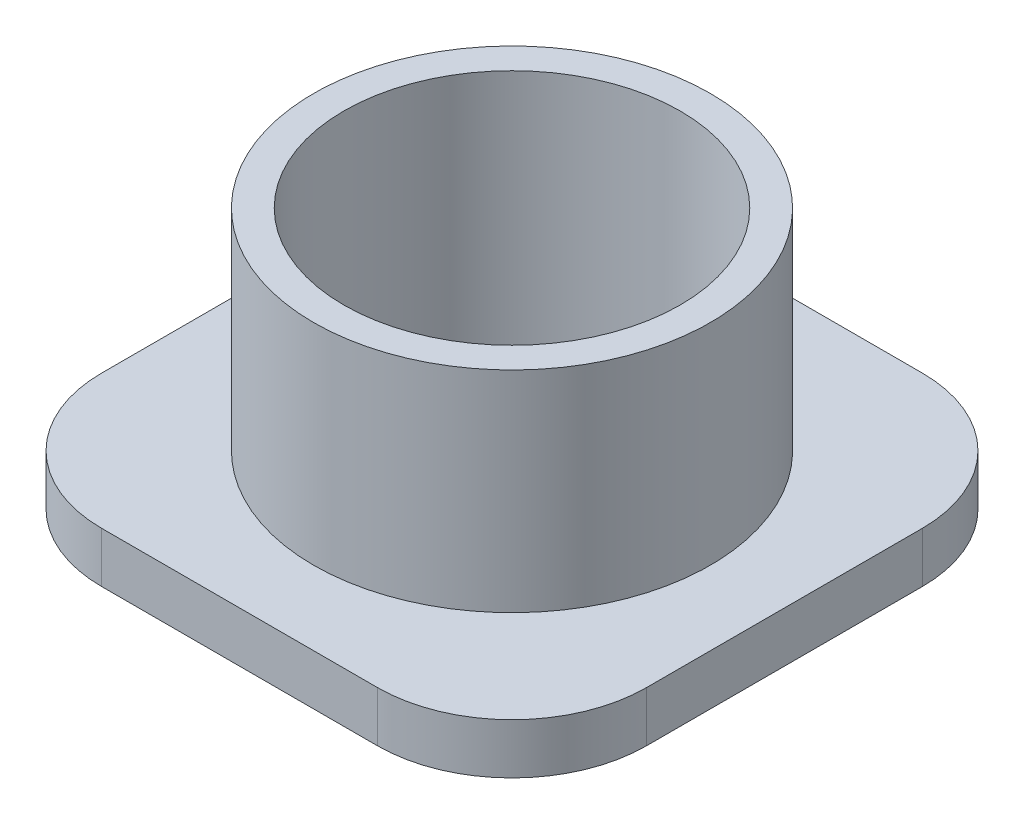
SolidWorks part; units mm, degrees
ref_plane "YZ" through (0, 0, 0) normal (0, 0, 1) x (1, 0, 0)
ref_plane "XY" through (0, 0, 0) normal (0, 1, 0) x (1, 0, 0)
ref_plane "XZ" through (0, 0, 0) normal (1, 0, 0) x (0, 0, -1)
sketch "Sketch1" plane through (0, 0, 0) normal (0, 1, 0) x (1, 0, 0)
  line L0 (-10.414, 20.574) -> (10.414, 20.574)
  line L1 (-20.574, 10.414) -> (-20.574, -10.414)
  line L2 (10.414, -20.574) -> (-10.414, -20.574)
  line L3 (20.574, -10.414) -> (20.574, 10.414)
  line L4 (0, 20.574) -> (0, 0) construction
  line L5 (0, 0) -> (20.574, 0) construction
  arc A0 (10.414, 20.574) -> (20.574, 10.414) centre (10.414, 10.414) cw
  arc A1 (-20.574, 10.414) -> (-10.414, 20.574) centre (-10.414, 10.414) cw
  arc A2 (-20.574, -10.414) -> (-10.414, -20.574) centre (-10.414, -10.414) ccw
  arc A3 (20.574, -10.414) -> (10.414, -20.574) centre (10.414, -10.414) cw
  dimension "D1" = 10.16
  dimension "D2" = 10.16
  dimension "D3" = 10.16
  dimension "D4" = 10.16
  dimension "D5" = 41.148
  dimension "D6" = 41.148
extrude "Base-Extrude" add sketch "Sketch1" along normal blind 3.81
sketch "Sketch2" plane through (0, 3.81, 0) normal (0, 1, 0) x (-1, 0, 0)
  circle A0 centre (0, 0) radius 14.986
  dimension "D1" = 29.972
extrude "Boss-Extrude1" add sketch "Sketch2" along normal blind 15.875
sketch "Sketch3" plane through (0, 19.685, 0) normal (0, 1, 0) x (-1, 0, 0)
  circle A0 centre (0, 0) radius 12.7
  dimension "D1" = 25.4
extrude "Cut-Extrude1" cut sketch "Sketch3" against normal through all
